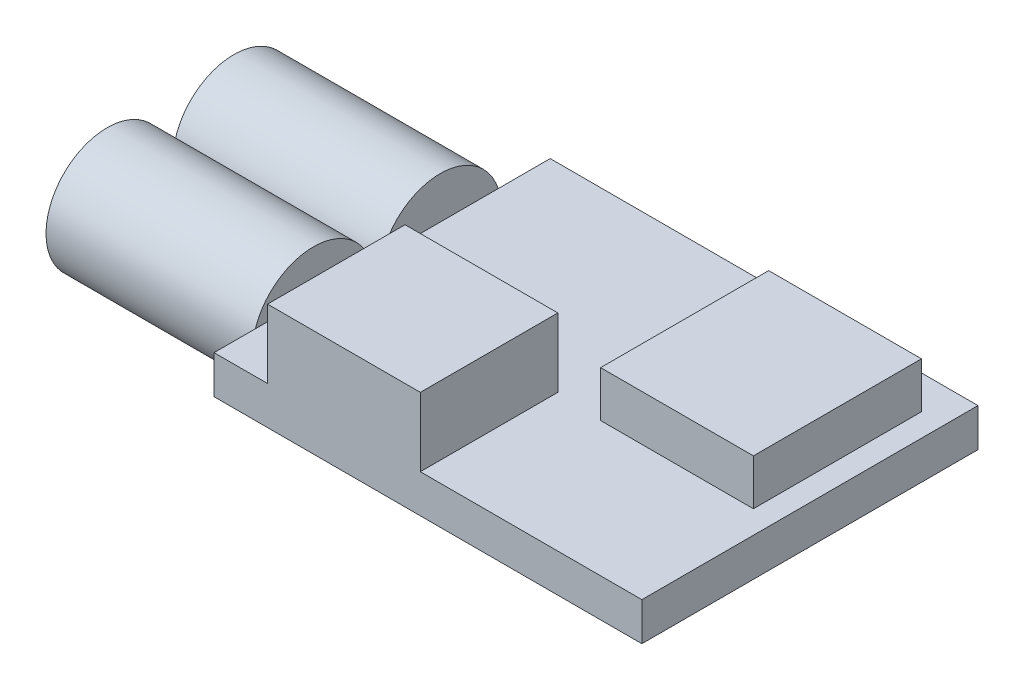
SolidWorks part; units mm, degrees
ref_plane "Front Plane" through (0, 0, 0) normal (0, 0, 1) x (1, 0, 0)
ref_plane "Top Plane" through (0, 0, 0) normal (0, 1, 0) x (1, 0, 0)
ref_plane "Right Plane" through (0, 0, 0) normal (1, 0, 0) x (0, 0, -1)
sketch "Sketch1" plane through (0, 0, 0) normal (0, 1, 0) x (1, 0, 0)
  line L1 (-14, 11) -> (14, 11)
  line L2 (-14, 11) -> (-14, -11)
  line L3 (-14, -11) -> (14, -11)
  line L4 (14, 11) -> (14, -11)
  point P4 (-14, 0)
  point P6 (0, 11)
  dimension "D1" = 28
  dimension "D2" = 22
extrude "Boss-Extrude1" add sketch "Sketch1" along normal blind 2.5
sketch "Sketch2" plane through (0, 2.5, 0) normal (0, 1, 0) x (1, 0, 0)
  line L0 (-14, -11) -> (14, -11) construction
  line L1 (-10.5, -11) -> (-0.5, -11)
  line L2 (-10.5, -11) -> (-10.5, -2)
  line L3 (-10.5, -2) -> (-0.5, -2)
  line L4 (-0.5, -11) -> (-0.5, -2)
  line L5 (-14, 11) -> (-14, -11) construction
  dimension "D1" = 10
  dimension "D2" = 9
  dimension "D3" = 3.5
extrude "Boss-Extrude2" add sketch "Sketch2" along normal blind 4.5
sketch "Sketch3" plane through (0, 2.5, 0) normal (0, 1, 0) x (1, 0, 0)
  line L0 (14, 11) -> (-14, 11) construction
  line L1 (2.5, 8.8) -> (12.5, 8.8)
  line L2 (2.5, 8.8) -> (2.5, -2.2)
  line L3 (2.5, -2.2) -> (12.5, -2.2)
  line L4 (12.5, 8.8) -> (12.5, -2.2)
  line L5 (14, -11) -> (14, 11) construction
  dimension "D1" = 10
  dimension "D2" = 11
  dimension "D3" = 2.2
  dimension "D4" = 1.5
extrude "Boss-Extrude3" add sketch "Sketch3" along normal blind 3
sketch "Sketch4" plane through (-14, 0, 0) normal (-1, 0, 0) x (0, 0, 1)
  line L0 (-11, 2.5) -> (-11, 0) construction
  line L1 (11, 2.5) -> (11, 0) construction
  circle A0 centre (-3.8, 1.25) radius 4
  circle A1 centre (4.5, 1.25) radius 4
  point P7 (-11, 1.25)
  dimension "D1" = 8
  dimension "D2" = 8
  dimension "D3" = 8.3
  dimension "D4" = 6.5
extrude "Boss-Extrude4" add sketch "Sketch4" along normal blind 13.5
